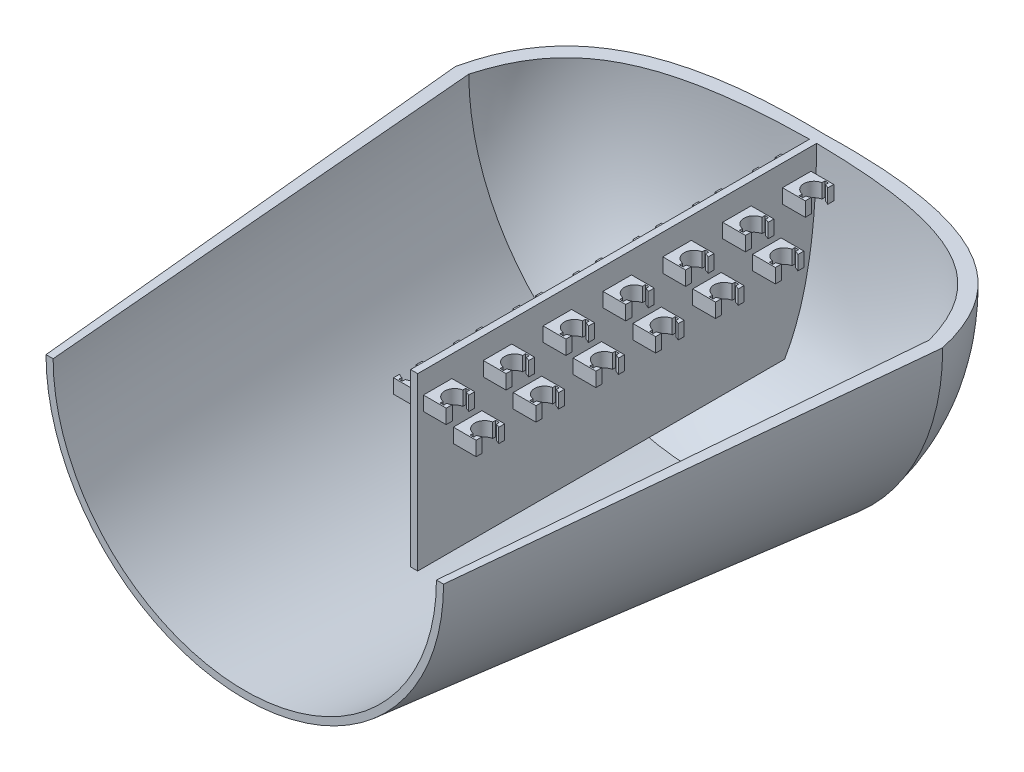
SolidWorks part; units mm, degrees
ref_plane "Front Plane" through (0, 0, 0) normal (0, 0, 1) x (1, 0, 0)
ref_plane "Top Plane" through (0, 0, 0) normal (0, 1, 0) x (1, 0, 0)
ref_plane "Right Plane" through (0, 0, 0) normal (1, 0, 0) x (0, 0, -1)
sketch "Sketch1" plane through (0, 0, 0) normal (0, 1, 0) x (1, 0, 0)
  line L1 (-1.5875, 88.9) -> (1.5875, 88.9)
  line L2 (-1.5875, 88.9) -> (-1.5875, -88.9)
  line L3 (-1.5875, -88.9) -> (1.5875, -88.9)
  line L4 (1.5875, 88.9) -> (1.5875, -88.9)
  line L5 (-1.5875, 88.9) -> (1.5875, -88.9) construction
  line L6 (-1.5875, -88.9) -> (1.5875, 88.9) construction
  point P0 (0, 0)
  dimension "D1" = 177.8
  dimension "D2" = 3.175
extrude "Boss-Extrude1" add sketch "Sketch1" along normal blind 76.2 contours L4 L3 L2 L1
sketch "Sketch2" plane through (1.5875, 0, 0) normal (1, 0, 0) x (0, 0, -1)
  line L0 (88.9, 76.2) -> (88.9, 0) construction
  line L1 (73.66, 66.675) -> (86.36, 66.675)
  line L2 (73.66, 66.675) -> (73.66, 60.325)
  line L3 (73.66, 60.325) -> (86.36, 60.325)
  line L4 (86.36, 66.675) -> (86.36, 60.325)
  line L6 (88.9, 76.2) -> (-88.9, 76.2) construction
  point P6 (86.36, 63.5)
  dimension "D1" = 6.35
  dimension "D2" = 12.7
  dimension "D3" = 2.54
  dimension "D4" = 12.7
extrude "Boss-Extrude2" add sketch "Sketch2" along normal blind 10.16
sketch "Sketch3" plane through (0, 66.675, 0) normal (0, 1, 0) x (1, 0, 0)
  line L2 (11.7475, 86.36) -> (11.7475, 73.66) construction
  line L3 (8.4137, 74.295) -> (10.0012, 74.295)
  line L4 (8.4137, 74.295) -> (8.4137, 85.725)
  line L5 (8.4137, 85.725) -> (10.0012, 85.725)
  line L6 (10.0012, 74.295) -> (10.0012, 85.725)
  line L7 (8.4137, 74.295) -> (10.0012, 85.725) construction
  line L8 (8.4137, 85.725) -> (10.0012, 74.295) construction
  line L10 (11.7475, 86.36) -> (1.5875, 86.36) construction
  circle A0 centre (9.2075, 80.01) radius 4.445
  point P8 (0, 0)
  point P9 (0, 0)
  point P10 (0, 0)
  point P11 (0, 0)
  line M4 (11.7475, 73.66) -> (11.7475, 86.36)
  dimension "D1" = 8.89
  dimension "D2" = 2.54
  dimension "D3" = 11.43
  dimension "D4" = 6.35
  dimension "D5" = 1.5875
extrude "Cut-Extrude1" cut sketch "Sketch3" against normal up to next (6.35 mm away) contours L4 A0 | A0 L4 L3 L6 | L6 A0 L4 | A0 L6 L5 L4 | L6 A0 M4
pattern_linear "LPattern2" count 7 spacing 26.67 along (0, 0, 1) of "Cut-Extrude1", "Boss-Extrude2"
sketch "Sketch4" plane through (1.5875, 0, 0) normal (1, 0, 0) x (0, 0, -1)
  line L1 (60.325, 47.625) -> (73.025, 47.625)
  line L2 (60.325, 47.625) -> (60.325, 41.275)
  line L3 (60.325, 41.275) -> (73.025, 41.275)
  line L4 (73.025, 47.625) -> (73.025, 41.275)
  line L7 (88.9, 76.2) -> (88.9, 0) construction
  line L8 (88.9, 76.2) -> (-88.9, 76.2) construction
  point P4 (66.675, 41.275)
  point P6 (73.025, 44.45)
  dimension "D1" = 12.7
  dimension "D2" = 6.35
  dimension "D3" = 31.75
  dimension "D4" = 22.225
extrude "Boss-Extrude3" add sketch "Sketch4" along normal blind 10.16 contours L3 L4 L1 L2
sketch "Sketch5" plane through (0, 47.625, 0) normal (0, 1, 0) x (1, 0, 0)
  line L1 (8.4137, 60.96) -> (10.0012, 60.96)
  line L2 (8.4137, 60.96) -> (8.4137, 72.39)
  line L3 (8.4137, 72.39) -> (10.0012, 72.39)
  line L4 (11.7475, 60.325) -> (11.7475, 73.025) construction
  line L5 (10.0012, 60.96) -> (10.0012, 72.39)
  line L6 (8.4137, 60.96) -> (10.0012, 72.39) construction
  line L7 (8.4137, 72.39) -> (10.0012, 60.96) construction
  circle A3 centre (9.2075, 66.675) radius 4.445
  point P4 (11.7475, 66.675)
  line M4 (11.7475, 60.325) -> (11.7475, 73.025)
  dimension "D4" = 8.89
  dimension "D1" = 1.5875
  dimension "D2" = 2.54
  dimension "D3" = 11.43
extrude "Cut-Extrude2" cut sketch "Sketch5" against normal up to next (6.35 mm away) contours L2 A3 | L5 A3 M4
pattern_linear "LPattern3" count 6 spacing 26.67 along (0, 0, 1) of "Cut-Extrude2", "Boss-Extrude3"
mirror "Mirror1" about plane through (0, 0, 0) normal (1, 0, 0) of "LPattern2", "Boss-Extrude2", "LPattern3", "Cut-Extrude1", "Boss-Extrude3", "Cut-Extrude2"
sketch "Sketch8" plane through (0, 76.2, 0) normal (0, 1, 0) x (1, 0, 0)
  line L0 (0, 88.9) -> (0, 94.0967)
  line L1 (-1.5875, 88.9) -> (1.5875, 88.9) construction
  line L2 (102.6251, 38.0799) -> (85.4148, -164.39)
  line L3 (85.4148, -164.39) -> (88.5898, -164.39)
  line L4 (88.5898, -164.39) -> (108.5802, 38.0799)
  line L5 (0, -98.5261) -> (0, 133.1629) construction
  spline S0 degree 3 poles (0, 88.9) (69.2009, 88.2897) (93.115, 72.1088) (102.6251, 38.0799) knots 0 0 0 0 1 1 1 1
  spline S1 degree 3 poles (0, 94.0967) (73.3564, 96.0186) (100.3075, 74.8069) (108.5802, 38.0799) knots 0 0 0 0 1 1 1 1
  dimension "D2" = 3.175
  dimension "D1" = 203.2
revolve "Revolve2" add sketch "Sketch8" angle 180 about L5
